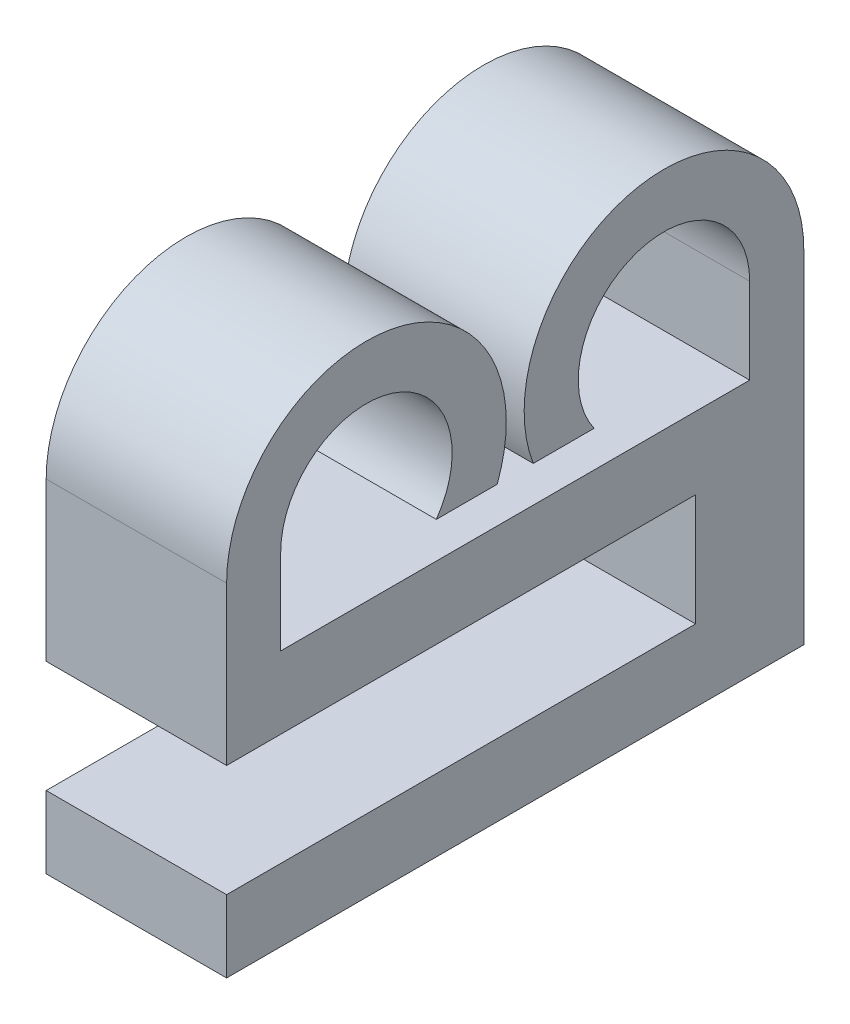
SolidWorks part; units mm, degrees
ref_plane "Front Plane" through (0, 0, 0) normal (0, 0, 1) x (1, 0, 0)
ref_plane "Top Plane" through (0, 0, 0) normal (0, 1, 0) x (1, 0, 0)
ref_plane "Right Plane" through (0, 0, 0) normal (1, 0, 0) x (0, 0, -1)
sketch "Sketch1" plane through (0, 0, 0) normal (1, 0, 0) x (0, 0, -1)
  line L0 (-6.4978, 0) -> (-6.4978, 2.375)
  line L1 (-7.9978, 0) -> (7.9978, 0)
  line L2 (-7.9978, 0) -> (-7.9978, -2)
  line L3 (-7.9978, -2) -> (7.9978, -2)
  line L4 (7.9978, 0) -> (7.9978, -2)
  line L5 (-2.1864, 1) -> (-0.5, 1)
  line L6 (-7.9978, 2.375) -> (-7.9978, 0)
  line L7 (7.9978, 0) -> (7.9978, 2.375)
  line L8 (0.5, 1) -> (2.1864, 1)
  line L9 (6.4978, 2.375) -> (6.4978, 0)
  arc A0 (-6.4978, 2.375) -> (-2.1864, 1) centre (-4.1228, 2.375) cw
  arc A1 (-0.5, 1) -> (-7.9978, 2.375) centre (-4.1228, 2.375) ccw
  arc A2 (7.9978, 2.375) -> (0.5, 1) centre (4.1228, 2.375) ccw
  arc A3 (2.1864, 1) -> (6.4978, 2.375) centre (4.1228, 2.375) cw
  point P4 (0, 0)
  dimension "D4" = 2.375
  dimension "D5" = 1
  dimension "D1" = 2
  dimension "D2" = 1
  dimension "D3" = 1.5
  dimension "D6" = 2.375
extrude "Boss-Extrude1" add sketch "Sketch1" along normal blind 5 contours L5 A1 L6 L1 L0 A0 | L4 L1 L2 L3 | L8 A3 L9 L1 L7 A2
ref_plane "Plane1" through (2.5, 0, 0) normal (1, 0, 0) x (0, 0, -1)
sketch "Sketch2" plane through (0, 0, 0) normal (-1, 0, 0) x (0, 0, 1)
  line L0 (-7.9978, -2) -> (-7.9978, -7.1)
  line L1 (-7.9978, -7.1) -> (7.9978, -7.1)
  line L2 (7.9978, -7.1) -> (7.9978, -5.1)
  line L3 (7.9978, -5.1) -> (-4.9978, -5.1)
  line L4 (-4.9978, -5.1) -> (-4.9978, -2)
  line L5 (7.9978, -2) -> (-7.9978, -2) construction
  line L6 (-4.9978, -2) -> (-7.9978, -2)
  line L7 (7.9978, 2.375) -> (7.9978, -2) construction
  dimension "D1" = 3.1
  dimension "D2" = 2
  dimension "D3" = 3
extrude "Boss-Extrude2" add sketch "Sketch2" against normal up to surface (5 mm away) up to face at (5, 2.0332, 0)
